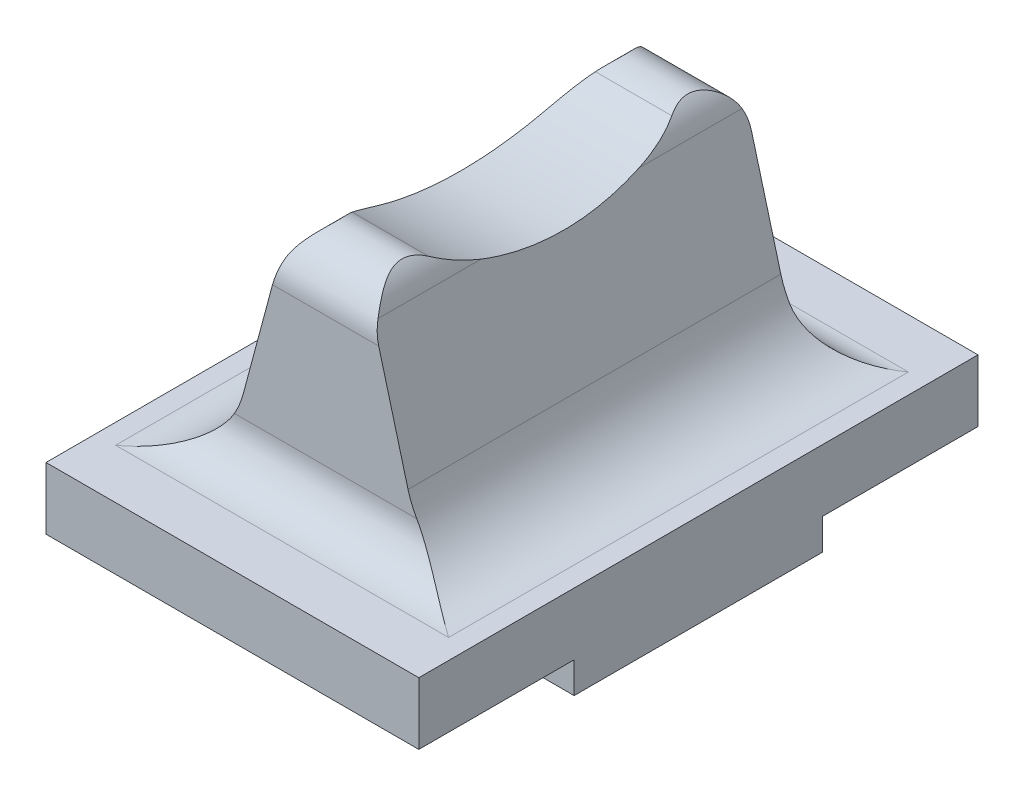
SolidWorks part; units mm, degrees
material "1.0050 (E295)"
ref_plane "Front Plane" through (0, 0, 0) normal (0, 0, 1) x (1, 0, 0)
ref_plane "Top Plane" through (0, 0, 0) normal (0, 1, 0) x (1, 0, 0)
ref_plane "Right Plane" through (0, 0, 0) normal (1, 0, 0) x (0, 0, -1)
sketch "Sketch1" plane through (0, 0, 0) normal (1, 0, 0) x (0, 0, -1)
  line L0 (-44.9665, 0) -> (44.9665, 0) construction
  line L1 (-20, 0) -> (20, 0)
  line L2 (20, 0) -> (20, 5)
  line L3 (20, 5) -> (45, 5)
  line L4 (45, 5) -> (45, 15)
  line L5 (45, 15) -> (-45, 15)
  line L6 (0, 23.3224) -> (0, -17.8419) construction
  line L7 (-45, 5) -> (-45, 15)
  line L8 (-20, 5) -> (-45, 5)
  line L9 (-20, 0) -> (-20, 5)
  point P4 (0, 0)
  point P8 (0, 0)
  point P16 (0, 15)
  dimension "D1" = 40
  dimension "D2" = 5
  dimension "D3" = 10
  dimension "D4" = 90
extrude "Boss-Extrude1" add sketch "Sketch1" along normal mid plane 60
sketch "Sketch4" plane through (0, 0, 0) normal (1, 0, 0) x (0, 0, -1)
  line L0 (0, -12.7359) -> (0, 89.5276) construction
  line L1 (30, 15) -> (30, 43)
  line L2 (45, 15) -> (-45, 15) construction
  line L3 (-30, 15) -> (-30, 43)
  line L4 (-20, 0) -> (20, 0) construction
  line L5 (-30, 15) -> (30, 15)
  arc A0 (30, 43) -> (19.5745, 49.1046) centre (23, 43) ccw
  arc A1 (19.5745, 49.1046) -> (-19.5745, 49.1046) centre (0, 83.9878) cw
  arc A2 (-30, 43) -> (-19.5745, 49.1046) centre (-23, 43) cw
  dimension "D1" = 40
  dimension "D2" = 7
  dimension "D3" = 60
  dimension "D4" = 43
extrude "Boss-Extrude2" add sketch "Sketch4" along normal mid plane 60
fillet "Fillet1" radius 7 2 edges at (0, 15, -30) (0, 15, 30)
sketch "Sketch5" plane through (0, 0, 45) normal (0, 0, 1) x (1, 0, 0)
  line L0 (0, -69.1588) -> (0, 69.1588) construction
  line L2 (7.7274, 46.0584) -> (13.2691, 25.3765)
  line L3 (30, 15) -> (-30, 15) construction
  line L4 (-7.7274, 46.0584) -> (-13.2691, 25.3765)
  line L5 (26.792, 15) -> (30, 15)
  line L6 (30, 15) -> (30, 50)
  line L7 (30, 50) -> (-30, 50)
  line L8 (-30, 15) -> (-30, 50)
  line L9 (-26.792, 15) -> (-30, 15)
  line L10 (-30, 43.9878) -> (30, 43.9878) construction
  arc A0 (7.7274, 46.0584) -> (-7.7274, 46.0584) centre (0, 43.9878) ccw
  arc A1 (-13.2691, 25.3765) -> (-26.792, 15) centre (-26.792, 29) cw
  arc A2 (13.2691, 25.3765) -> (26.792, 15) centre (26.792, 29) ccw
  point P4 (0, 0)
  point P15 (0, 51)
  point P23 (-16.0495, 15)
  point P26 (16.0495, 15)
  line M11 (30, 15) -> (-30, 15)
  dimension "D2" = 14
  dimension "D3" = 30
  dimension "D1" = 8
extrude "Cut-Extrude1" cut sketch "Sketch5" against normal through all contours A1 L4 A0 L7 L8 M11 | L2 A2 L6 L7 A0 M11
